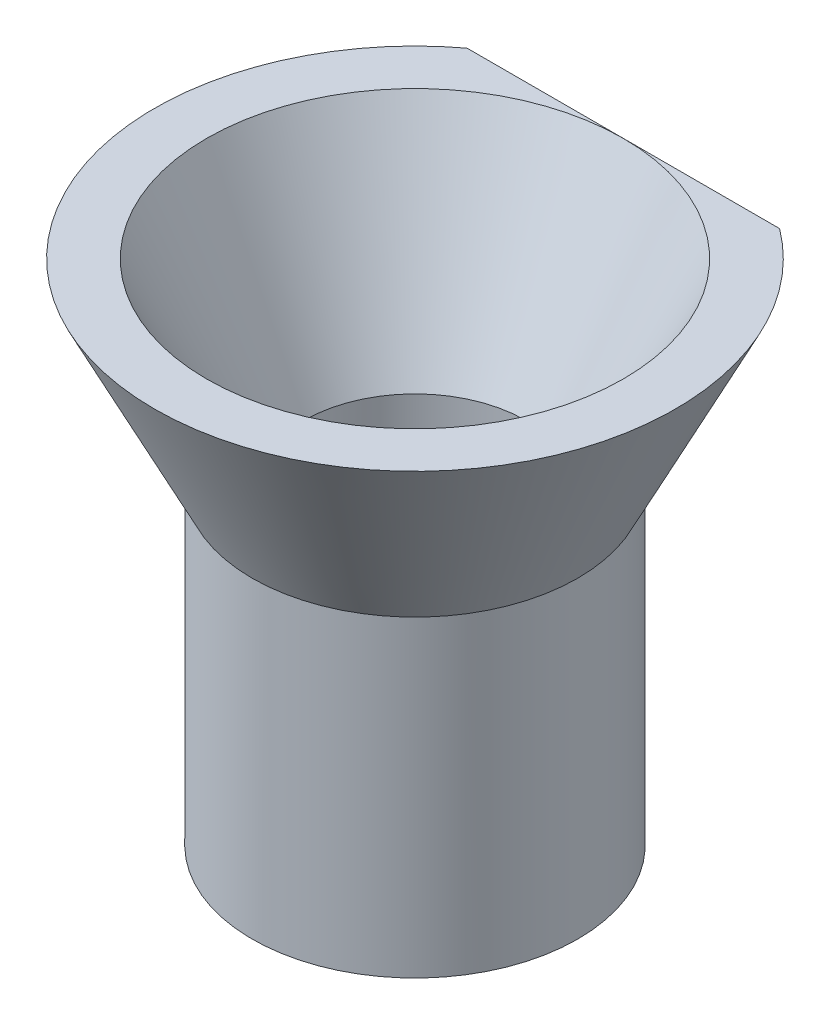
SolidWorks part; units mm, degrees
ref_plane "Alzado" through (0, 0, 0) normal (0, 0, 1) x (1, 0, 0)
ref_plane "Planta" through (0, 0, 0) normal (0, 1, 0) x (1, 0, 0)
ref_plane "Vista lateral" through (0, 0, 0) normal (1, 0, 0) x (0, 0, -1)
sketch "Croquis2" plane through (0, 0, 0) normal (0, 0, 1) x (1, 0, 0)
  line L0 (0, 0) -> (-4.25, 0) construction
  line L1 (-4.25, 0) -> (-8, 7.5)
  line L2 (-8, 7.5) -> (0, 7.5) construction
  line L3 (0, 7.5) -> (0, 0) construction
  line L4 (-8, 7.5) -> (-10, 7.5)
  line L5 (-10, 7.5) -> (-6.25, 0)
  line L6 (-6.25, 0) -> (-4.25, 0)
  dimension "D1" = 7.5
  dimension "D2" = 8
  dimension "D3" = 4.25
  dimension "D4" = 2
  dimension "D5" = 2
revolve "Revolución1" add sketch "Croquis2" angle 360 about L3
sketch "Croquis3" plane through (0, 0, 0) normal (0, -1, 0) x (1, 0, 0)
  circle A0 centre (0, 0) radius 4.25
  circle A1 centre (0, 0) radius 6.25
  dimension "D1" = 8.5
  dimension "D2" = 2
extrude "Saliente-Extruir1" add sketch "Croquis3" along normal blind 12
sketch "Croquis4" plane through (0, 7.5, 0) normal (0, 1, 0) x (1, 0, 0)
  line L0 (-10.9771, 8) -> (10.9771, 8)
  line L1 (10.9771, 8) -> (0, 12.6091)
  line L2 (0, 12.6091) -> (-10.9771, 8)
  point P3 (0, 8)
extrude "Cortar-Extruir1" cut sketch "Croquis4" against normal blind 10
